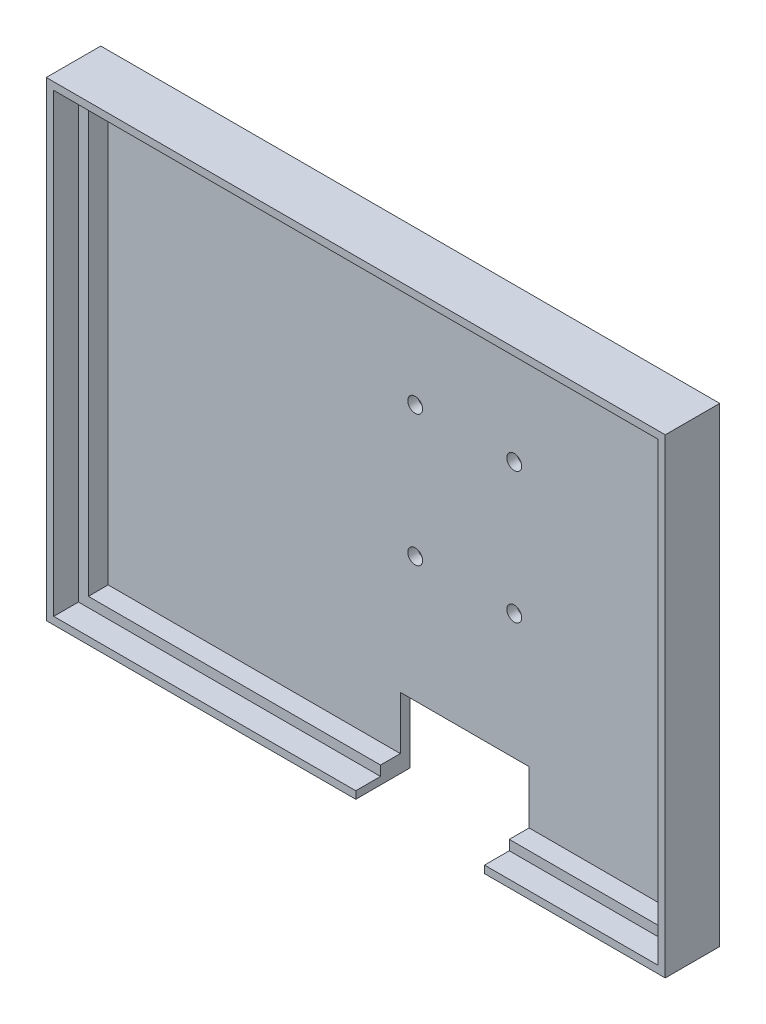
SolidWorks part; units mm, degrees
ref_plane "Front Plane" through (0, 0, 0) normal (0, 0, 1) x (1, 0, 0)
ref_plane "Top Plane" through (0, 0, 0) normal (0, 1, 0) x (1, 0, 0)
ref_plane "Right Plane" through (0, 0, 0) normal (1, 0, 0) x (0, 0, -1)
sketch "Sketch1" plane through (0, 0, 0) normal (0, 0, 1) x (1, 0, 0)
  line L1 (-62.5, -47.5) -> (62.5, -47.5)
  line L2 (-62.5, -47.5) -> (-62.5, 47.5)
  line L3 (-62.5, 47.5) -> (62.5, 47.5)
  line L4 (62.5, -47.5) -> (62.5, 47.5)
  line L5 (-62.5, -47.5) -> (62.5, 47.5) construction
  line L6 (-62.5, 47.5) -> (62.5, -47.5) construction
  line L7 (-59, -44) -> (59, -44)
  line L8 (-59, -44) -> (-59, 44)
  line L9 (-59, 44) -> (59, 44)
  line L10 (59, -44) -> (59, 44)
  line L11 (-59, -44) -> (59, 44) construction
  line L12 (-59, 44) -> (59, -44) construction
  point P0 (0, 0)
  point P6 (0, 0)
  dimension "D1" = 125
  dimension "D2" = 95
  dimension "D3" = 118
  dimension "D4" = 88
extrude "Boss-Extrude1" add sketch "Sketch1" along normal blind 4 contours L8 L7 L10 L9 | L2 L1 L4 L3
sketch "Sketch2" plane through (0, 0, 0) normal (0, 0, -1) x (-1, 0, 0)
  line L1 (-62.5, -47.5) -> (62.5, -47.5)
  line L2 (-62.5, -47.5) -> (-62.5, 47.5)
  line L3 (-62.5, 47.5) -> (62.5, 47.5)
  line L4 (62.5, -47.5) -> (62.5, 47.5)
  line L5 (-62.5, -47.5) -> (62.5, 47.5) construction
  line L6 (-62.5, 47.5) -> (62.5, -47.5) construction
  point P0 (0, 0)
extrude "Boss-Extrude2" add sketch "Sketch2" along normal blind 2
sketch "Sketch3" plane through (0, 0, 4) normal (0, 0, 1) x (1, 0, 0)
  line L1 (-62.5, -47.5) -> (62.5, -47.5)
  line L2 (-62.5, -47.5) -> (-62.5, 47.5)
  line L3 (-62.5, 47.5) -> (62.5, 47.5)
  line L4 (62.5, -47.5) -> (62.5, 47.5)
  line L5 (-62.5, -47.5) -> (62.5, 47.5) construction
  line L6 (-62.5, 47.5) -> (62.5, -47.5) construction
  line L7 (61, -46) -> (-61, -46)
  line L8 (61, -46) -> (61, 46)
  line L9 (61, 46) -> (-61, 46)
  line L10 (-61, -46) -> (-61, 46)
  line L11 (61, -46) -> (-61, 46) construction
  line L12 (61, 46) -> (-61, -46) construction
  point P0 (0, 0)
  point P7 (0, 0)
  dimension "D1" = 122
  dimension "D2" = 92
extrude "Boss-Extrude3" add sketch "Sketch3" along normal blind 5
sketch "Sketch5" plane through (0, 0, -2) normal (0, 0, -1) x (-1, 0, 0)
  line L0 (0, 47.5) -> (0, -47.5) construction
  line L1 (62.5, 47.5) -> (-62.5, 47.5) construction
  line L2 (-62.5, -47.5) -> (62.5, -47.5) construction
  line L3 (-13, 21.5) -> (-13, -12.5) construction
  line L5 (0, -12.5) -> (-26, -12.5)
  line L6 (0, -12.5) -> (0, 21.5)
  line L7 (0, 21.5) -> (-26, 21.5)
  line L8 (-26, -12.5) -> (-26, 21.5)
  circle A0 centre (-23, 18.5) radius 1.5
  circle A1 centre (-23, -8) radius 1.5
  circle A2 centre (-3, -8) radius 1.5
  circle A3 centre (-3, 18.5) radius 1.5
  point P6 (0, -12.5)
  point P15 (0, 0)
  point P16 (0, 0)
  dimension "D4" = 3
  dimension "D7" = 3
  dimension "D1" = 60
  dimension "D2" = 34
  dimension "D3" = 26
  dimension "D5" = 3
  dimension "D6" = 3
  dimension "D8" = 26.5
extrude "Cut-Extrude1" cut sketch "Sketch5" against normal blind 26.5 contours A3 | A0 | A2 | A1
sketch "Sketch7" plane through (0, 0, -2) normal (0, 0, -1) x (-1, 0, 0)
  line L0 (-62.5, -47.5) -> (62.5, -47.5) construction
  line L1 (0, -47.5) -> (-26, -47.5)
  line L2 (0, -47.5) -> (0, -33.2874)
  line L3 (0, -33.2874) -> (-26, -33.2874)
  line L4 (-26, -47.5) -> (-26, -33.2874)
  dimension "D1" = 26
extrude "Cut-Extrude2" cut sketch "Sketch7" against normal blind 26.5
